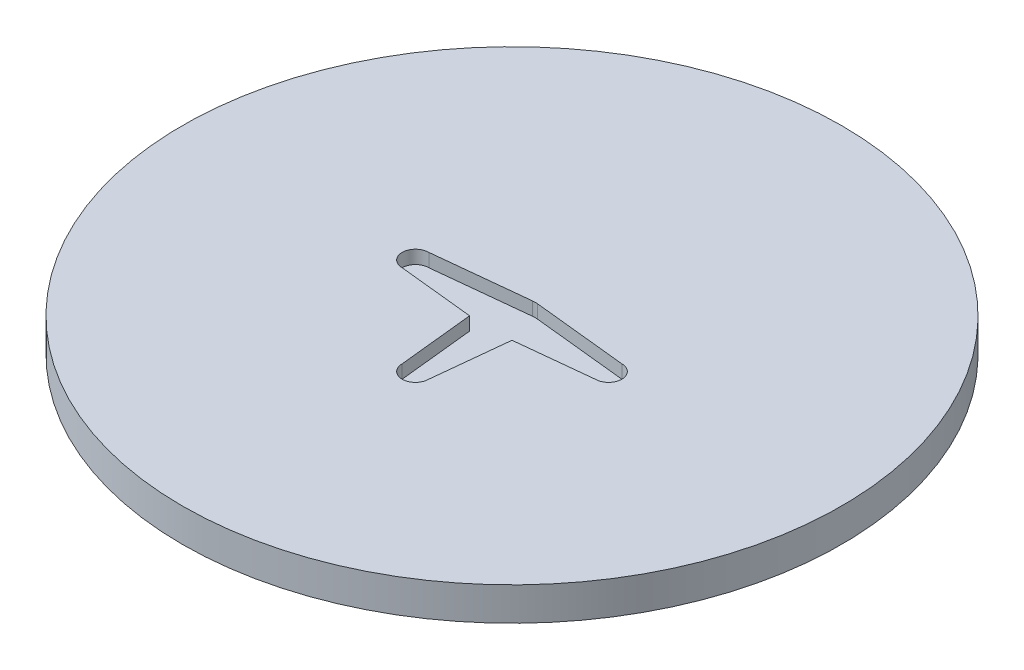
SolidWorks part; units mm, degrees
ref_plane "Front Plane" through (0, 0, 0) normal (0, 0, 1) x (1, 0, 0)
ref_plane "Top Plane" through (0, 0, 0) normal (0, 1, 0) x (1, 0, 0)
ref_plane "Right Plane" through (0, 0, 0) normal (1, 0, 0) x (0, 0, -1)
sketch "Sketch1" plane through (0, 0, 0) normal (0, 1, 0) x (1, 0, 0)
  circle A0 centre (0, 0) radius 49.5
  dimension "D1" = 99
extrude "Boss-Extrude1" add sketch "Sketch1" along normal blind 5
sketch "Sketch2" plane through (0, 5, 0) normal (0, 1, 0) x (1, 0, 0)
  line L1 (14.5, 2) -> (0.3647, 3.4809)
  line L2 (14.5, -2) -> (3.1854, -3.1854)
  line L3 (2, -14.5) -> (3.1854, -3.1854)
  line L4 (-2, -14.5) -> (-3.1854, -3.1854)
  line L5 (-14.5, -2) -> (-3.1854, -3.1854)
  line L6 (-14.5, 2) -> (-0.3647, 3.4809)
  arc A1 (14.5, -2) -> (14.5, 2) centre (14.5, 0) ccw
  arc A9 (-2, -14.5) -> (2, -14.5) centre (0, -14.5) ccw
  arc A10 (-14.5, 2) -> (-14.5, -2) centre (-14.5, 0) ccw
  arc A11 (0.3647, 3.4809) -> (-0.3647, 3.4809) centre (0, 0) ccw
  point P18 (0, 0)
  point P23 (0, 0)
  point P24 (0, 0)
  point P38 (0, 0)
  dimension "D2" = 4
  dimension "D3" = 3
extrude "Cut-Extrude1" cut sketch "Sketch2" against normal blind 2
sketch "Sketch3" plane through (0, 0, 0) normal (0, -1, 0) x (1, 0, 0)
  ellipse E0 centre (0, 0) end of major axis (0, -25) minor radius 7.5 (7.1837, 7.1837) -> (-7.1837, 7.1837) ccw
  ellipse E1 centre (0, 0) end of major axis (-25, 0) minor radius 7.5 (7.1837, -7.1837) -> (7.1837, 7.1837) ccw
  ellipse E2 centre (0, 0) end of major axis (0, -25) minor radius 7.5 (-7.1837, -7.1837) -> (7.1837, -7.1837) ccw
  ellipse E3 centre (0, 0) end of major axis (-25, 0) minor radius 7.5 (-7.1837, 7.1837) -> (-7.1837, -7.1837) ccw
  point P15 (0, 0)
extrude "Cut-Extrude3" cut sketch "Sketch3" against normal blind 2.5
sketch "Sketch4" plane through (0, 2.5, 0) normal (0, -1, 0) x (1, 0, 0)
  arc A0 (25, 0) -> (17.6777, 17.6777) centre (0, 0) ccw
  arc A1 (0, 25) -> (-17.6777, 17.6777) centre (0, 0) ccw
  arc A2 (-25, 0) -> (-17.6777, -17.6777) centre (0, 0) ccw
  arc A3 (0, -25) -> (17.6777, -17.6777) centre (0, 0) ccw
  ellipse E0 centre (0, 0) end of major axis (0, -25) minor radius 7.5 (6.0742, 14.6644) -> (0, 25) ccw
  ellipse E1 centre (0, 0) end of major axis (-25, 0) minor radius 7.5 (14.6644, -6.0742) -> (25, 0) ccw
  ellipse E2 centre (0, 0) end of major axis (0, -25) minor radius 7.5 (-6.0742, -14.6644) -> (0, -25) ccw
  ellipse E3 centre (0, 0) end of major axis (-25, 0) minor radius 7.5 (-14.6644, 6.0742) -> (-25, 0) ccw
  ellipse E4 centre (0, 0) end of major axis (-17.6777, -17.6777) minor radius 7.5 (17.6777, 17.6777) -> (6.0742, 14.6644) ccw
  ellipse E5 centre (0, 0) end of major axis (-17.6777, 17.6777) minor radius 7.5 (-17.6777, 17.6777) -> (-14.6644, 6.0742) ccw
  ellipse E6 centre (0, 0) end of major axis (-17.6777, -17.6777) minor radius 7.5 (-17.6777, -17.6777) -> (-6.0742, -14.6644) ccw
  ellipse E7 centre (0, 0) end of major axis (-17.6777, 17.6777) minor radius 7.5 (17.6777, -17.6777) -> (14.6644, -6.0742) ccw
  point P15 (0, 0)
  point P47 (0, 0)
extrude "Cut-Extrude4" cut sketch "Sketch4" along normal blind 1.5
sketch "Sketch5" plane through (0, 2.5, 0) normal (0, -1, 0) x (1, 0, 0)
  circle A0 centre (0, 0) radius 2.5
extrude "Boss-Extrude2" add sketch "Sketch5" along normal up to surface (2.5 mm away) up to face at (0, 0, 0)
